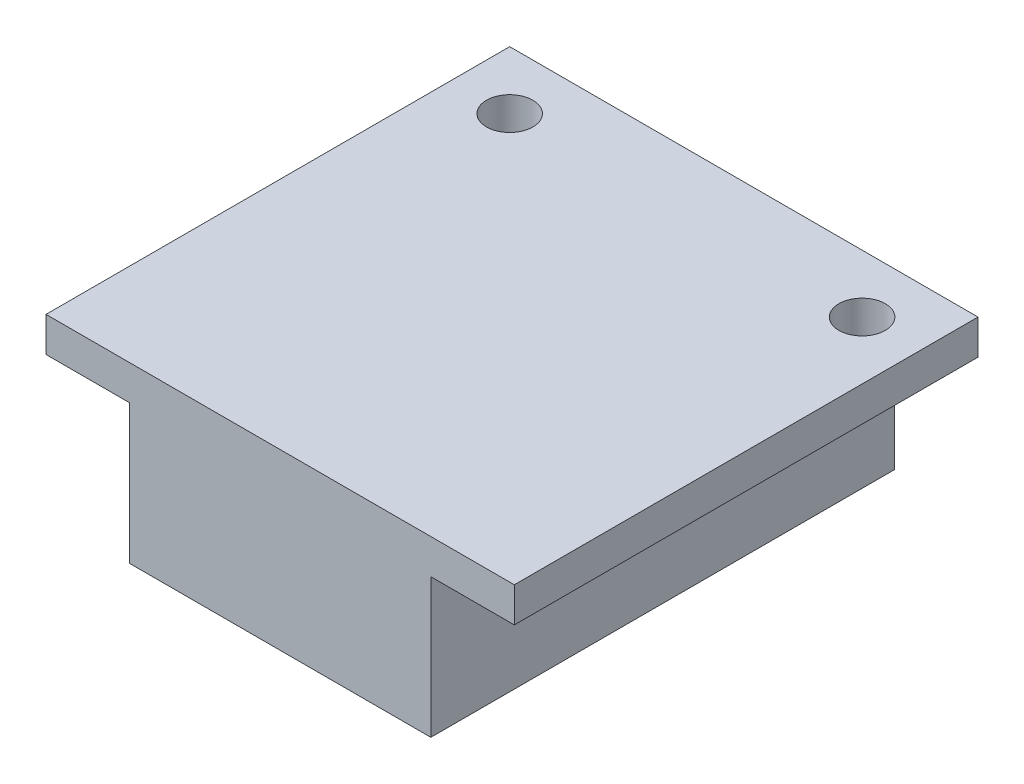
SolidWorks part; units mm, degrees
ref_plane "前视基准面" through (0, 0, 0) normal (0, 0, 1) x (1, 0, 0)
ref_plane "上视基准面" through (0, 0, 0) normal (0, 1, 0) x (1, 0, 0)
ref_plane "右视基准面" through (0, 0, 0) normal (1, 0, 0) x (0, 0, -1)
sketch "草图1" plane through (0, 0, 0) normal (0, 0, 1) x (1, 0, 0)
  line L1 (-16.2597, 1.0522) -> (3.9403, 1.0522)
  line L2 (-16.2597, 1.0522) -> (-16.2597, -0.4478)
  line L3 (-16.2597, -0.4478) -> (3.9403, -0.4478)
  line L4 (3.9403, 1.0522) -> (3.9403, -0.4478)
  dimension "D1" = 1.5
  dimension "D2" = 20.2
extrude "凸台-拉伸1" add sketch "草图1" against normal blind 20
sketch "草图2" plane through (0, 0, 0) normal (0, 0, 1) x (1, 0, 0)
  line L0 (0.3403, -6.4478) -> (0.3403, -0.4478)
  line L1 (-12.6597, -6.4478) -> (-12.6597, -0.4478)
  line L2 (0.3403, -0.4478) -> (0.3403, -6.4478)
  line L3 (-16.2597, -0.4478) -> (3.9403, -0.4478) construction
  line L4 (0.3403, -6.4478) -> (-12.6597, -6.4478)
  line L5 (0.3403, -0.4478) -> (-12.6597, -0.4478)
  line L6 (-12.6597, -0.4478) -> (-12.6597, -6.4478)
  line L7 (-12.6597, -6.4478) -> (0.3403, -6.4478)
  line M6 (-16.2597, -0.4478) -> (3.9403, -0.4478)
  dimension "D3" = 6
extrude "凸台-拉伸2" add sketch "草图2" against normal blind 20 contours L4 L0 L1 M6
sketch "草图3" plane through (0, -0.4478, 0) normal (0, -1, 0) x (-1, 0, 0)
  circle A0 centre (-1.4403, 17.5) radius 1
  circle A1 centre (13.7597, 17.5) radius 1
  dimension "D4" = 2
  dimension "D5" = 2
extrude "切除-拉伸1" cut sketch "草图3" against normal through all
